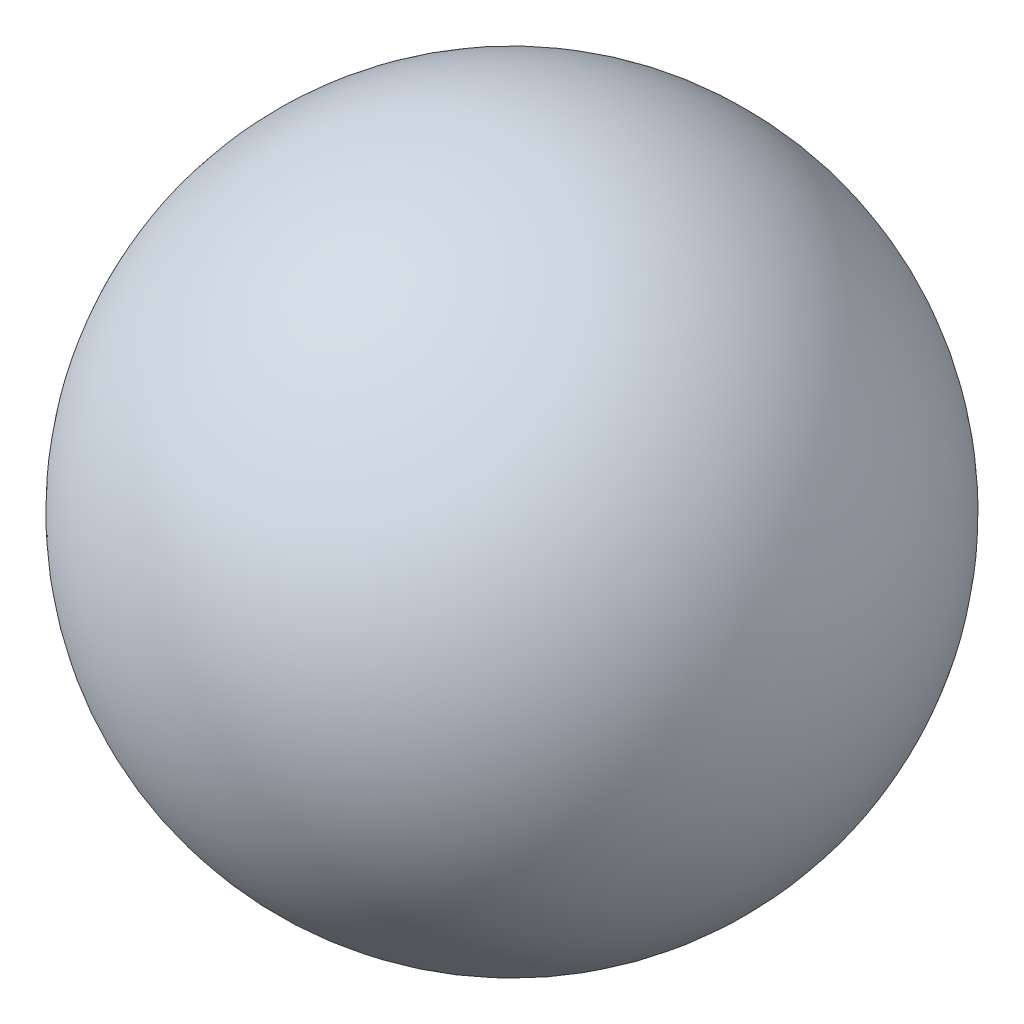
SolidWorks part; units mm, degrees
ref_plane "Front Plane" through (0, 0, 0) normal (0, 0, 1) x (1, 0, 0)
ref_plane "Top Plane" through (0, 0, 0) normal (0, 1, 0) x (1, 0, 0)
ref_plane "Right Plane" through (0, 0, 0) normal (1, 0, 0) x (0, 0, -1)
sketch "Sketch1" plane through (0, 0, 0) normal (0, 0, 1) x (1, 0, 0)
  line L0 (-12, 0) -> (12, 0)
  arc A0 (-12, 0) -> (12, 0) centre (0, 0) ccw
  point P3 (0, 0)
  dimension "D1" = 24
revolve "Revolve1" add sketch "Sketch1" angle 360 about L0
